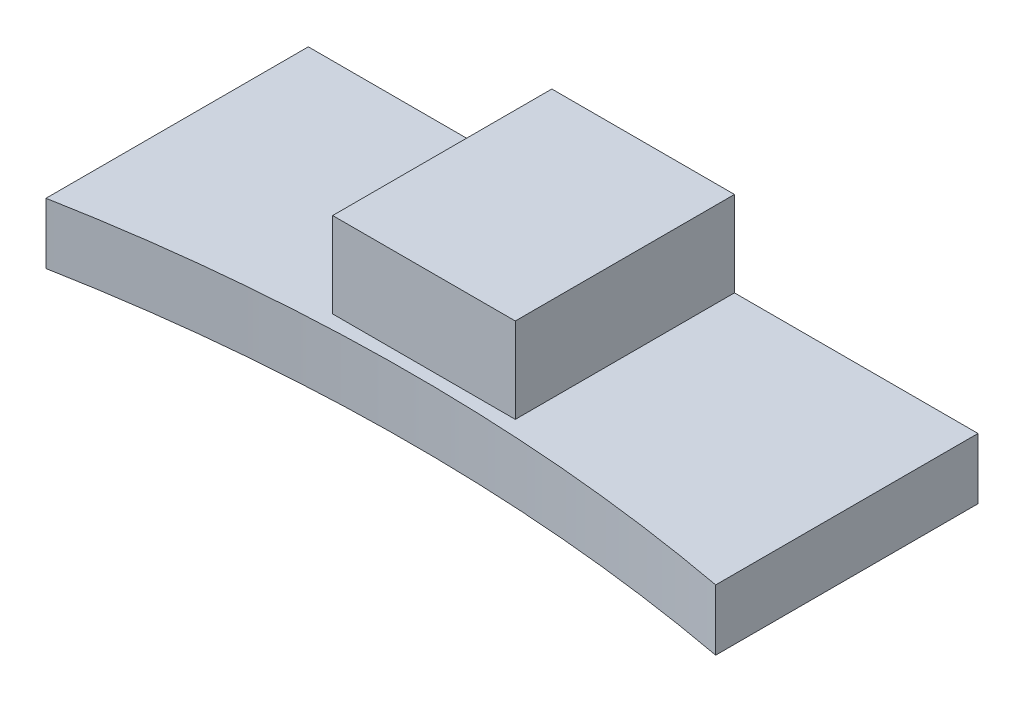
SolidWorks part; units mm, degrees
ref_plane "Front Plane" through (0, 0, 0) normal (0, 0, 1) x (1, 0, 0)
ref_plane "Top Plane" through (0, 0, 0) normal (0, 1, 0) x (1, 0, 0)
ref_plane "Right Plane" through (0, 0, 0) normal (1, 0, 0) x (0, 0, -1)
sketch "Sketch1" plane through (0, 0, 0) normal (0, 1, 0) x (1, 0, 0)
  line L0 (0, 0) -> (0, 21.5424)
  line L1 (0, 21.5424) -> (55, 21.5424)
  line L2 (55, 21.5424) -> (55, 0)
  line L3 (0, 2.5424) -> (55, 2.5424) construction
  arc A0 (0, 0) -> (55, 0) centre (27.5, -147.4576) cw
  dimension "D1" = 150
  dimension "D2" = 55
  dimension "D3" = 19
extrude "Boss-Extrude1" add sketch "Sketch1" along normal blind 5
sketch "Sketch2" plane through (0, 5, 0) normal (0, 1, 0) x (1, 0, 0)
  line L0 (55, 21.5424) -> (0, 21.5424) construction
  line L1 (20, 21.5424) -> (35, 21.5424)
  line L2 (20, 21.5424) -> (20, 3.5424)
  line L3 (20, 3.5424) -> (35, 3.5424)
  line L4 (35, 21.5424) -> (35, 3.5424)
  line L5 (0, 21.5424) -> (0, 0) construction
  dimension "D1" = 15
  dimension "D2" = 20
  dimension "D3" = 18
extrude "Boss-Extrude2" add sketch "Sketch2" along normal blind 7
sketch "Sketch3" plane through (0, 0, -21.5424) normal (0, 0, -1) x (-1, 0, 0)
  line L0 (-55, 0) -> (0, 0) construction
  line L1 (-35, 12) -> (-35, 5) construction
  circle A0 centre (-27.5, 6.5) radius 4.5
  dimension "D1" = 9
  dimension "D2" = 6.5
  dimension "D3" = 7.5
extrude "Cut-Extrude2" cut sketch "Sketch3" against normal blind 4
hole_wizard "Tap Drill for M8x1.25 Tap1" positions "Sketch5" profile "Sketch4" hole size "M8x1.25" standard "ANSI Metric"
sketch "Sketch5" plane through (0, 0, -17.5424) normal (0, 0, -1) x (-1, 0, 0)
  point P0 (-27.5, 6.5)
sketch "Sketch4" plane through (27.5, 6.5, -17.5424) normal (1, 0, 0) x (0, 1, 0)
  line L0 (0, 0) -> (0, 8)
  line L1 (0, 8) -> (3.4, 8)
  line L2 (3.4, 8) -> (3.4, 0)
  line L5 (3.4, 0) -> (0, 0)
  line L10 (0, 8) -> (-3.4, 8) construction
  line L11 (0, -6.35) -> (0, 107.95) construction
  dimension "Hole Dia." = 6.8
  dimension "Hole Depth" = 8
  dimension "Drill Angle" = 180
